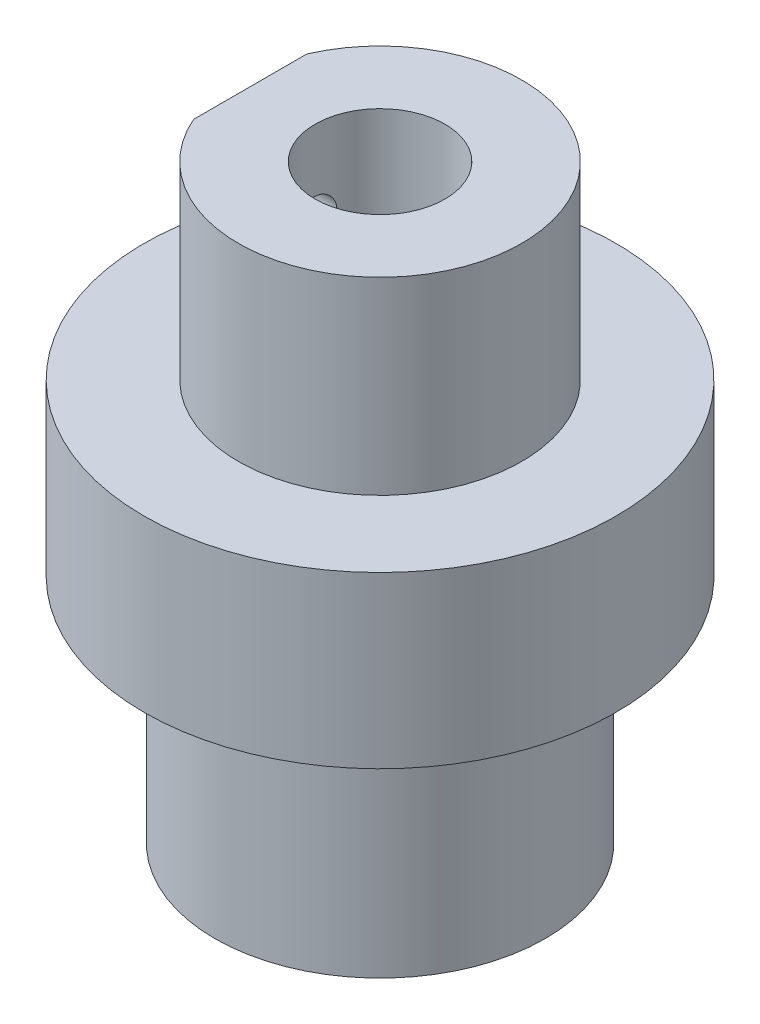
SolidWorks part; units mm, degrees
material "2.0402 (CuZn40Pb2)"
ref_plane "Front Plane" through (0, 0, 0) normal (0, 0, 1) x (1, 0, 0)
ref_plane "Top Plane" through (0, 0, 0) normal (0, 1, 0) x (1, 0, 0)
ref_plane "Right Plane" through (0, 0, 0) normal (1, 0, 0) x (0, 0, -1)
sketch "Sketch5" plane through (0, 0, 0) normal (0, 1, 0) x (1, 0, 0)
  circle A0 centre (0, 0) radius 7
extrude "Boss-Extrude2" add sketch "Sketch5" along normal blind 9.8
sketch "Sketch6" plane through (0, 9.8, 0) normal (0, 1, 0) x (1, 0, 0)
  circle A0 centre (0, 0) radius 10
extrude "Boss-Extrude3" add sketch "Sketch6" along normal blind 7.2
hole_wizard "M8 Tapped Hole2" positions "Sketch8" profile "Sketch9" tap size "M8" standard "DIN"
sketch "Sketch8" plane through (0, 0, 0) normal (0, -1, 0) x (-1, 0, 0)
  point P0 (0, 0)
sketch "Sketch9" plane through (0, 0, 0) normal (1, 0, 0) x (0, 0, -1)
  line L0 (0, 0) -> (0, 19.0429)
  line L1 (0, 19.0429) -> (3.4, 17)
  line L2 (3.4, 17) -> (3.4, 0)
  line L5 (3.4, 0) -> (0, 0)
  line L10 (0, 19.0429) -> (-3.4, 17) construction
  line L11 (0, -6.35) -> (0, 107.95) construction
  dimension "Tap Drill Dia." = 6.8
  dimension "Tap Drill Depth" = 17
  dimension "Drill Angle" = 118
cosmetic thread "Hole Thread2" parameters "D1"=12, "D2"=8
sketch "Sketch11" plane through (0, 17, 0) normal (0, 1, 0) x (1, 0, 0)
  line L0 (-5.5, 2.3979) -> (-5.5, -2.3979)
  arc A0 (-5.5, -2.3979) -> (-5.5, 2.3979) centre (0, 0) ccw
  dimension "D1" = 5.5
extrude "Boss-Extrude5" add sketch "Sketch11" along normal blind 8
sketch "Sketch12" plane through (0, 25, 0) normal (0, 1, 0) x (1, 0, 0)
  circle A0 centre (0, 0) radius 2.75
extrude "Cut-Extrude6" cut sketch "Sketch12" against normal blind 9
hole_wizard "M2 Tapped Hole1" positions "Sketch13" profile "Sketch15" tap size "M2" standard "DIN"
sketch "Sketch13" plane through (-5.5, 0, 0) normal (-1, 0, 0) x (0, 0, 1)
  point P0 (0, 21.5521)
sketch "Sketch15" plane through (-5.5, 21.5521, 0) normal (0, 1, 0) x (0, 0, 1)
  line L0 (0, 0) -> (0, 5.6807)
  line L1 (0, 5.6807) -> (0.8, 5.2)
  line L2 (0.8, 5.2) -> (0.8, 0)
  line L5 (0.8, 0) -> (0, 0)
  line L10 (0, 5.6807) -> (-0.8, 5.2) construction
  line L11 (0, -6.35) -> (0, 107.95) construction
  dimension "Tap Drill Dia." = 1.6
  dimension "Tap Drill Depth" = 5.2
  dimension "Drill Angle" = 118
cosmetic thread "Hole Thread3" parameters "D1"=4, "D2"=2
